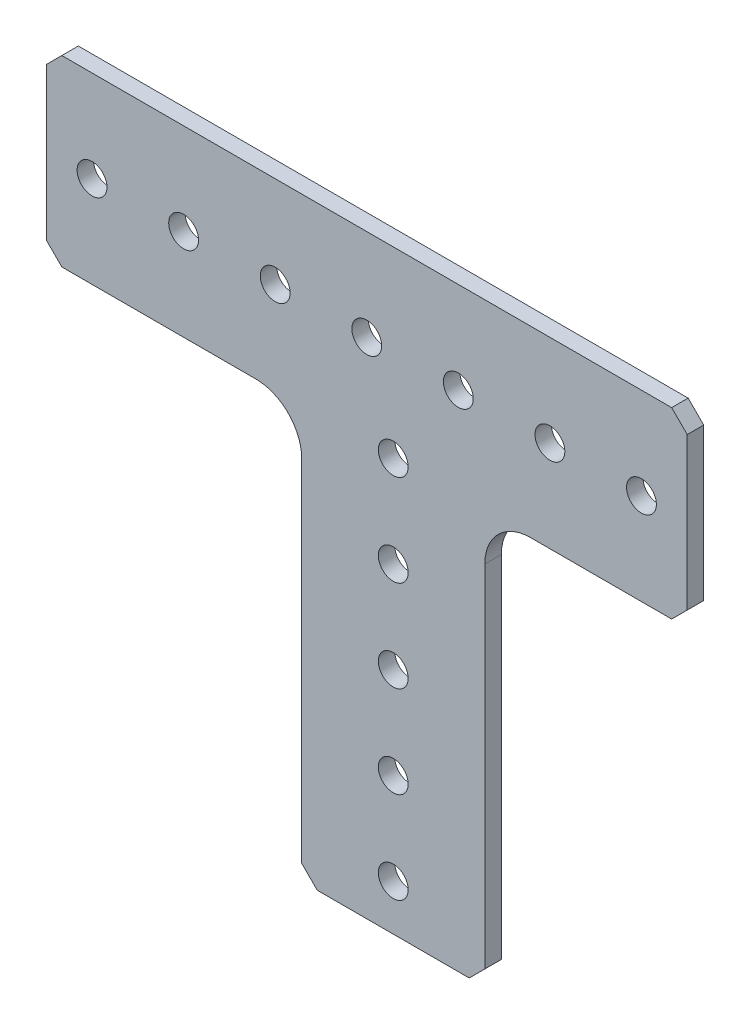
SolidWorks part; units mm, degrees
ref_plane "Front Plane" through (0, 0, 0) normal (0, 0, 1) x (1, 0, 0)
ref_plane "Top Plane" through (0, 0, 0) normal (0, 1, 0) x (1, 0, 0)
ref_plane "Right Plane" through (0, 0, 0) normal (1, 0, 0) x (0, 0, -1)
ref_plane "Plane1" through (0, 0, 2.286) normal (0, 0, 1) x (1, 0, 0)
sketch "Sketch1" plane through (0, 0, 2.286) normal (0, 0, 1) x (1, 0, 0)
  line L0 (16.3725, -54.991) -> (16.3725, -6.35)
  line L1 (22.7225, 0) -> (42.291, 0)
  line L2 (42.291, 0) -> (44.45, 2.159)
  line L3 (44.45, 2.159) -> (44.45, 23.241)
  line L4 (44.45, 23.241) -> (42.291, 25.4)
  line L5 (42.291, 25.4) -> (-42.291, 25.4)
  line L6 (-42.291, 25.4) -> (-44.45, 23.241)
  line L7 (-44.45, 23.241) -> (-44.45, 2.159)
  line L8 (-44.45, 2.159) -> (-42.291, 0)
  line L9 (-42.291, 0) -> (-15.3775, 0)
  line L10 (-9.0275, -6.35) -> (-9.0275, -54.991)
  line L11 (-9.0275, -54.991) -> (-6.8685, -57.15)
  line L12 (-6.8685, -57.15) -> (14.2135, -57.15)
  line L13 (14.2135, -57.15) -> (16.3725, -54.991)
  line L14 (3.6725, 0) -> (3.6725, -68.4923) construction
  line L15 (0, 12.7) -> (0, 32.8297) construction
  circle A0 centre (3.6725, -38.1) radius 2.0701
  circle A1 centre (3.6725, -12.7) radius 2.0701
  circle A2 centre (38.1, 12.7) radius 2.0701
  circle A3 centre (12.7, 12.7) radius 2.0701
  circle A4 centre (-12.7, 12.7) radius 2.0701
  circle A5 centre (-38.1, 12.7) radius 2.0701
  circle A6 centre (-25.4, 12.7) radius 2.0701
  circle A7 centre (0, 12.7) radius 2.0701
  circle A8 centre (25.4, 12.7) radius 2.0701
  circle A9 centre (3.6725, 0) radius 2.0701
  circle A10 centre (3.6725, -25.4) radius 2.0701
  circle A11 centre (3.6725, -50.8) radius 2.0701
  arc A12 (16.3725, -6.35) -> (22.7225, 0) centre (22.7225, -6.35) cw
  arc A13 (-15.3775, 0) -> (-9.0275, -6.35) centre (-15.3775, -6.35) cw
  dimension "D1" = 4.1402
  dimension "D18" = 6.35
  dimension "D19" = 6.35
  dimension "D2" = 12.7
  dimension "D3" = 25.4
  dimension "D4" = 38.1
  dimension "D5" = 42.291
  dimension "D6" = 44.45
  dimension "D7" = 12.7
  dimension "D8" = 25.4
  dimension "D9" = 38.1
  dimension "D10" = 42.291
  dimension "D11" = 2.159
  dimension "D12" = 12.7
  dimension "D13" = 23.241
  dimension "D14" = 12.7
  dimension "D15" = 25.4
  dimension "D16" = 2.159
  dimension "D17" = 2.159
  dimension "D20" = 57.15
  dimension "D21" = 3.6725
extrude "Boss-Extrude1" add sketch "Sketch1" against normal blind 2.286
